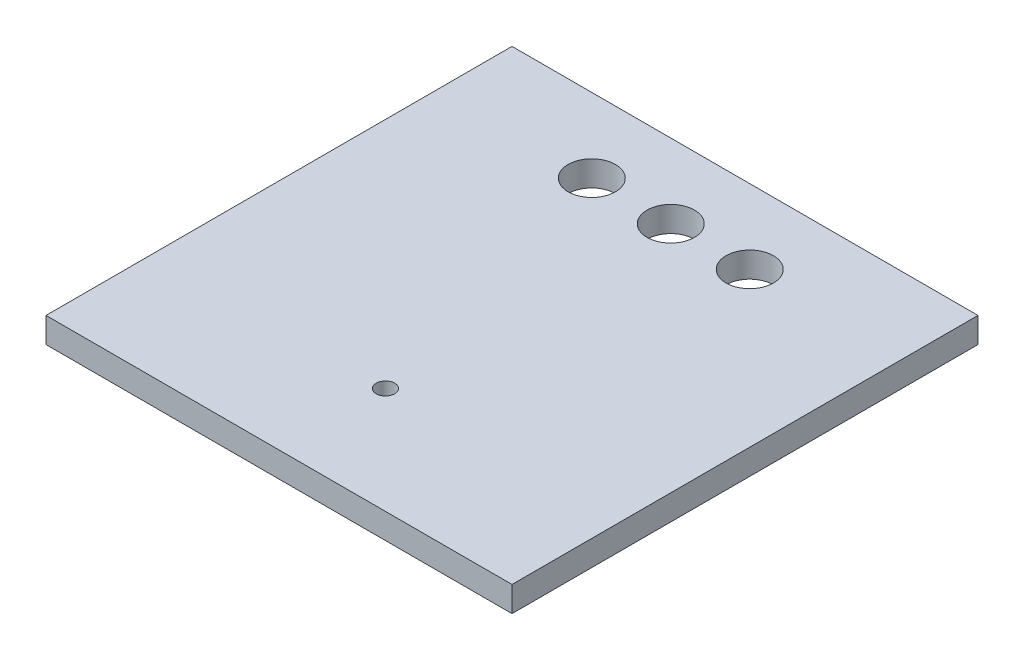
SolidWorks part; units mm, degrees
material "Custom Plastic"
ref_plane "Front Plane" through (0, 0, 0) normal (0, 0, 1) x (1, 0, 0)
ref_plane "Top Plane" through (0, 0, 0) normal (0, 1, 0) x (1, 0, 0)
ref_plane "Right Plane" through (0, 0, 0) normal (1, 0, 0) x (0, 0, -1)
sketch "Sketch1" plane through (0, 0, 0) normal (0, 1, 0) x (1, 0, 0)
  line L1 (-7.493, -7.493) -> (7.493, -7.493)
  line L2 (-7.493, -7.493) -> (-7.493, 7.493)
  line L3 (-7.493, 7.493) -> (7.493, 7.493)
  line L4 (7.493, -7.493) -> (7.493, 7.493)
  line L5 (-7.493, -7.493) -> (7.493, 7.493) construction
  line L6 (-7.493, 7.493) -> (7.493, -7.493) construction
  point P0 (0, 0)
  dimension "D1" = 14.986
  dimension "D2" = 14.986
extrude "Boss-Extrude1" add sketch "Sketch1" along normal blind 0.8128
ref_plane "PlaneforHoles" through (0, 2.54, 0) normal (0, 1, 0) x (1, 0, 0)
sketch "Sketch2" plane through (0, 2.54, 0) normal (0, 1, 0) x (1, 0, 0)
  line L0 (-12.0125, 5.1058) -> (12.6218, 5.1058) construction
  line L1 (0, -10.7727) -> (0, 10.7727) construction
  line L2 (-11.7813, -4.0702) -> (12.6218, -4.0702) construction
  circle A1 centre (0, 5.1058) radius 2.54 construction
  circle A2 centre (0, 5.1058) radius 0.762
  circle A3 centre (-2.54, 5.1058) radius 0.762
  circle A4 centre (2.54, 5.1058) radius 0.762
  circle A5 centre (0, -4.0702) radius 0.2972
extrude "Cut-Extrude1" cut sketch "Sketch2" against normal blind 8.4328 contours A3 | A2 | A4 | A5
equation "\"D2@Sketch1\"=\"D1@Sketch1\""
